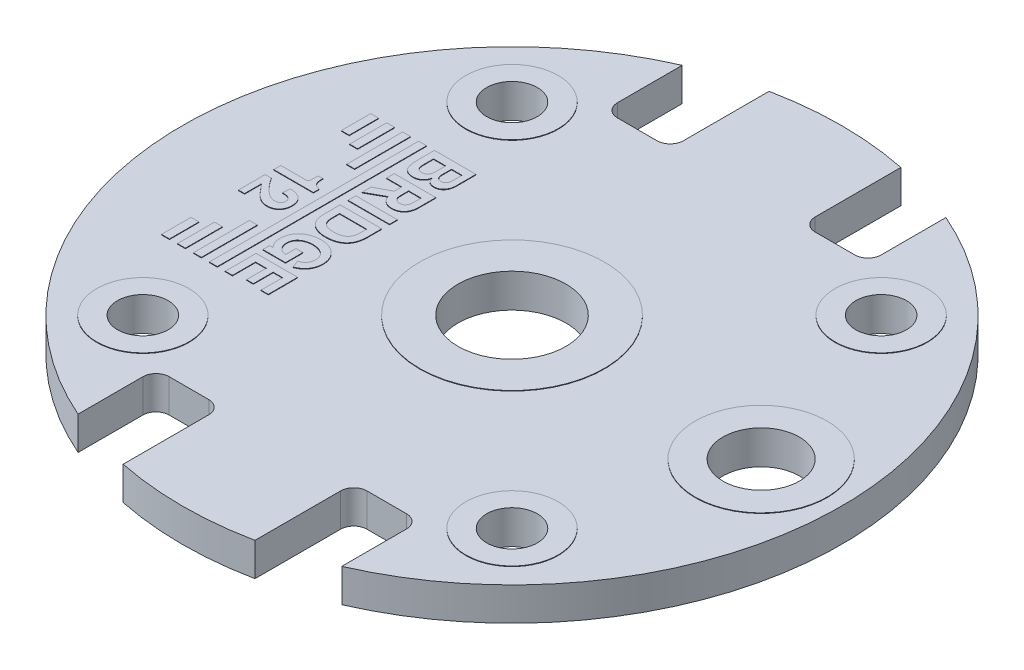
SolidWorks part; units mm, degrees
material "C110 COPPER"
ref_plane "Front Plane" through (0, 0, 0) normal (0, 0, 1) x (1, 0, 0)
ref_plane "Top Plane" through (0, 0, 0) normal (0, 1, 0) x (1, 0, 0)
ref_plane "Right Plane" through (0, 0, 0) normal (1, 0, 0) x (0, 0, -1)
sketch "Sketch1" plane through (0, 0, 0) normal (0, 1, 0) x (1, 0, 0)
  line L0 (-6.35, 14.5497) -> (-6.35, 11.43)
  line L1 (-5.715, 10.795) -> (-3.81, 10.795)
  line L2 (-3.175, 11.43) -> (-3.175, 15.5543)
  line L3 (0, 19.0474) -> (0, -17.3756) construction
  line L4 (-23.6625, 0) -> (27.7174, 0) construction
  line L5 (3.175, 11.43) -> (3.175, 15.5543)
  line L6 (5.715, 10.795) -> (3.81, 10.795)
  line L7 (6.35, 14.5497) -> (6.35, 11.43)
  line L8 (6.35, -14.5497) -> (6.35, -11.43)
  line L9 (5.715, -10.795) -> (3.81, -10.795)
  line L10 (3.175, -11.43) -> (3.175, -15.5543)
  line L11 (-3.175, -11.43) -> (-3.175, -15.5543)
  line L12 (-5.715, -10.795) -> (-3.81, -10.795)
  line L13 (-6.35, -14.5497) -> (-6.35, -11.43)
  arc A0 (-6.35, 14.5497) -> (-6.35, -14.5497) centre (0, 0) ccw
  arc A2 (-3.81, 10.795) -> (-3.175, 11.43) centre (-3.81, 11.43) ccw
  arc A3 (-6.35, 11.43) -> (-5.715, 10.795) centre (-5.715, 11.43) ccw
  arc A4 (3.81, 10.795) -> (3.175, 11.43) centre (3.81, 11.43) cw
  arc A5 (6.35, 11.43) -> (5.715, 10.795) centre (5.715, 11.43) cw
  arc A6 (6.35, -11.43) -> (5.715, -10.795) centre (5.715, -11.43) ccw
  arc A7 (3.81, -10.795) -> (3.175, -11.43) centre (3.81, -11.43) ccw
  arc A8 (-6.35, -11.43) -> (-5.715, -10.795) centre (-5.715, -11.43) cw
  arc A9 (-3.81, -10.795) -> (-3.175, -11.43) centre (-3.81, -11.43) cw
  arc A10 (3.175, 15.5543) -> (-3.175, 15.5543) centre (0, 0) ccw
  arc A11 (6.35, -14.5497) -> (6.35, 14.5497) centre (0, 0) ccw
  arc A12 (-3.175, -15.5543) -> (3.175, -15.5543) centre (0, 0) ccw
  dimension "D1" = 31.75
  dimension "D2" = 3.175
  dimension "D5" = 0.635
  dimension "D3" = 6.35
  dimension "D4" = 10.795
extrude "Boss-Extrude1" add sketch "Sketch1" along normal mid plane 1.6
sketch "Sketch12" plane through (0, 0.8, 0) normal (0, 1, 0) x (1, 0, 0)
  circle A0 centre (0, 0) radius 2.6
  dimension "D1" = 5.2
extrude "Cut-Extrude2" cut sketch "Sketch12" against normal through all
hole_wizard "#2 Clearance Hole1" positions "Sketch4" profile "Sketch5" hole size "#2" standard "ANSI Inch" end condition up to next
sketch "Sketch4" plane through (0, 0.8, 0) normal (0, 1, 0) x (1, 0, 0)
  line L1 (-8.89, 8.89) -> (8.89, 8.89)
  line L2 (-8.89, 8.89) -> (-8.89, -8.89)
  line L3 (-8.89, -8.89) -> (8.89, -8.89)
  line L4 (8.89, 8.89) -> (8.89, -8.89)
  line L5 (-8.89, 8.89) -> (8.89, -8.89) construction
  line L6 (-8.89, -8.89) -> (8.89, 8.89) construction
  point P1 (-8.89, 8.89)
  point P2 (8.89, -8.89)
  point P5 (-8.89, -8.89)
  point P6 (8.89, 8.89)
  point P70 (0, 0)
  dimension "D1" = 17.78
  dimension "D2" = 17.78
sketch "Sketch5" plane through (-8.89, 0.8, -8.89) normal (1, 0, 0) x (0, 0, 1)
  line L0 (0, 0) -> (0, 1.6)
  line L1 (0, 1.6) -> (1.2192, 1.6)
  line L2 (1.2192, 1.6) -> (1.2192, 0)
  line L5 (1.2192, 0) -> (0, 0)
  line L11 (0, -6.35) -> (0, 107.95) construction
  dimension "Thru Hole Dia." = 2.4384
  dimension "Thru Hole Depth" = 1.6
sketch "Sketch6" plane through (0, 0.8, 0) normal (0, 1, 0) x (1, 0, 0)
  line L0 (-21.8912, 0) -> (24.3968, 0) construction
  circle A3 centre (12, 0) radius 1.8415
  dimension "D1" = 3.683
  dimension "D2" = 12
extrude "Cut-Extrude1" cut sketch "Sketch6" against normal through all
sketch "Sketch8" plane through (0, 0.8, 0) normal (0, 1, 0) x (1, 0, 0)
  circle A0 centre (-8.89, 8.89) radius 2.2225
  circle A1 centre (8.89, 8.89) radius 2.2225
  circle A2 centre (-8.89, -8.89) radius 2.2225
  circle A3 centre (8.89, -8.89) radius 2.2225
  circle A4 centre (0, 0) radius 4.445
  circle A5 centre (12, 0) radius 3.175
  circle A19 centre (0, 0) radius 2.6 construction
  circle A20 centre (0, 0) radius 2.6
  circle A21 centre (-8.89, -8.89) radius 1.2192 construction
  circle A22 centre (-8.89, -8.89) radius 1.2192
  circle A23 centre (-8.89, 8.89) radius 1.2192 construction
  circle A24 centre (-8.89, 8.89) radius 1.2192
  circle A25 centre (8.89, 8.89) radius 1.2192 construction
  circle A26 centre (8.89, 8.89) radius 1.2192
  circle A27 centre (12, 0) radius 1.8415 construction
  circle A28 centre (12, 0) radius 1.8415
  circle A29 centre (8.89, -8.89) radius 1.2192 construction
  circle A30 centre (8.89, -8.89) radius 1.2192
  dimension "D1" = 4.445
  dimension "D2" = 8.89
  dimension "D3" = 6.35
extrude "Boss-Extrude6" add sketch "Sketch8" along normal blind 0.0254
sketch "Sketch10" plane through (0, 0.8, 0) normal (0, 1, 0) x (1, 0, 0)
  line L0 (-8.4106, 4.6318) -> (-8.4106, 4.143)
  line L1 (-7.8263, 4.1458) -> (-7.8263, 4.6318)
  line L2 (-7.8263, 4.6318) -> (-8.4106, 4.6318)
  line L3 (-7.5454, 4.6318) -> (-7.5454, 4.1852)
  line L4 (-7.0397, 4.1852) -> (-7.0397, 4.6318)
  line L5 (-7.0397, 4.6318) -> (-7.5454, 4.6318)
  line L6 (-6.7419, 5.0083) -> (-6.7419, 4.0672)
  line L7 (-7.6437, 3.8143) -> (-7.6494, 3.8143)
  line L8 (-8.7421, 4.1571) -> (-8.7421, 5.0083)
  line L9 (-8.7421, 5.0083) -> (-6.7419, 5.0083)
  line L10 (-7.6746, 2.6963) -> (-7.6746, 2.2861)
  line L11 (-7.0734, 2.3423) -> (-7.0734, 2.6963)
  line L12 (-7.0734, 2.6963) -> (-7.6746, 2.6963)
  line L13 (-6.7419, 3.0727) -> (-6.7419, 2.2384)
  line L14 (-7.9359, 1.9603) -> (-8.7421, 1.5136)
  line L15 (-8.7421, 1.5136) -> (-8.7421, 1.949)
  line L16 (-8.7421, 1.949) -> (-8.0061, 2.3367)
  line L17 (-8.0061, 2.3367) -> (-8.0061, 2.6963)
  line L18 (-8.0061, 2.6963) -> (-8.7421, 2.6963)
  line L19 (-8.7421, 2.6963) -> (-8.7421, 3.0727)
  line L20 (-8.7421, 3.0727) -> (-6.7419, 3.0727)
  line L21 (-6.7419, 1.2215) -> (-6.7419, 0.8451)
  line L22 (-6.7419, 0.8451) -> (-8.7421, 0.8451)
  line L23 (-8.7421, 0.8451) -> (-8.7421, 1.2215)
  line L24 (-8.7421, 1.2215) -> (-6.7419, 1.2215)
  line L25 (-8.3938, 0.0894) -> (-8.3938, -0.2534)
  line L26 (-7.0903, -0.2449) -> (-7.0903, 0.0894)
  line L27 (-7.0903, 0.0894) -> (-8.3938, 0.0894)
  line L28 (-6.7419, 0.4658) -> (-6.7419, -0.2365)
  line L29 (-8.7421, -0.3068) -> (-8.7421, 0.4658)
  line L30 (-8.7421, 0.4658) -> (-6.7419, 0.4658)
  line L31 (-7.9808, -2.9175) -> (-7.9808, -2.423)
  line L32 (-7.9808, -2.423) -> (-7.6494, -2.423)
  line L33 (-7.6494, -2.423) -> (-7.6494, -3.2602)
  line L34 (-7.6494, -3.2602) -> (-8.7421, -3.2602)
  line L35 (-8.7421, -3.2602) -> (-8.7421, -2.9343)
  line L36 (-8.7421, -2.9343) -> (-8.5708, -2.9343)
  line L37 (-7.2785, -3.2602) -> (-7.4218, -2.909)
  line L38 (-6.7419, -3.5807) -> (-6.7419, -4.9965)
  line L39 (-6.7419, -4.9965) -> (-7.0903, -4.9965)
  line L40 (-7.0903, -4.9965) -> (-7.0903, -3.9571)
  line L41 (-7.0903, -3.9571) -> (-7.5454, -3.9571)
  line L42 (-7.5454, -3.9571) -> (-7.5454, -4.9123)
  line L43 (-7.5454, -4.9123) -> (-7.8769, -4.9123)
  line L44 (-7.8769, -4.9123) -> (-7.8769, -3.9571)
  line L45 (-7.8769, -3.9571) -> (-8.3938, -3.9571)
  line L46 (-8.3938, -3.9571) -> (-8.3938, -5.0696)
  line L47 (-8.3938, -5.0696) -> (-8.7421, -5.0696)
  line L48 (-8.7421, -5.0696) -> (-8.7421, -3.5807)
  line L49 (-8.7421, -3.5807) -> (-6.7419, -3.5807)
  line L50 (-10.4829, 0.8387) -> (-10.4829, 1.1421)
  line L51 (-10.4829, 1.1421) -> (-10.2525, 1.1421)
  line L52 (-10.2525, 1.1421) -> (-10.2525, 1.0859)
  line L53 (-9.9014, 0.6168) -> (-9.9014, 0.3358)
  line L54 (-9.9014, 0.3358) -> (-11.8117, 0.3358)
  line L55 (-11.8117, 0.3358) -> (-11.8117, 0.6786)
  line L56 (-11.8117, 0.6786) -> (-10.6711, 0.6786)
  line L57 (-11.5139, -0.5406) -> (-11.5139, -1.3665)
  line L58 (-11.5139, -1.3665) -> (-11.8117, -1.3665)
  line L59 (-11.8117, -1.3665) -> (-11.8117, -0.0743)
  line L60 (-11.8117, -0.0743) -> (-11.5139, -0.0743)
  line L61 (-10.6318, -0.417) -> (-10.6065, -0.0743)
  line L62 (-9.8937, -2.3704) -> (-10.2778, -2.3704)
  line L63 (-10.2778, -2.3704) -> (-10.2778, -5.068)
  line L64 (-10.2778, -5.068) -> (-9.8937, -5.068)
  line L65 (-9.8937, -5.068) -> (-9.8937, -2.3704)
  line L66 (-10.6619, -3.283) -> (-11.0461, -3.283)
  line L67 (-11.0461, -3.283) -> (-11.0461, -5.068)
  line L68 (-11.0461, -5.068) -> (-10.6619, -5.068)
  line L69 (-10.6619, -5.068) -> (-10.6619, -3.283)
  line L70 (-11.4303, -3.6479) -> (-11.8144, -3.6479)
  line L71 (-11.8144, -3.6479) -> (-11.8144, -5.068)
  line L72 (-11.8144, -5.068) -> (-11.4303, -5.068)
  line L73 (-11.4303, -5.068) -> (-11.4303, -3.6479)
  line L74 (-9.8937, 5.0104) -> (-10.2778, 5.0104)
  line L75 (-10.2778, 5.0104) -> (-10.2778, 2.3128)
  line L76 (-10.2778, 2.3128) -> (-9.8937, 2.3128)
  line L77 (-9.8937, 2.3128) -> (-9.8937, 5.0104)
  line L78 (-10.6619, 5.0104) -> (-11.0461, 5.0104)
  line L79 (-11.0461, 5.0104) -> (-11.0461, 3.2254)
  line L80 (-11.0461, 3.2254) -> (-10.6619, 3.2254)
  line L81 (-10.6619, 3.2254) -> (-10.6619, 5.0104)
  line L82 (-11.4303, 5.0104) -> (-11.8144, 5.0104)
  line L83 (-11.8144, 5.0104) -> (-11.8144, 3.5904)
  line L84 (-11.8144, 3.5904) -> (-11.4303, 3.5904)
  line L85 (-11.4303, 3.5904) -> (-11.4303, 5.0104)
  line L86 (-9.1255, 5.0104) -> (-9.5095, 5.0104)
  line L87 (-9.5095, 5.0104) -> (-9.5095, -5.0679)
  line L88 (-9.5095, -5.0679) -> (-9.1255, -5.0679)
  line L89 (-9.1255, -5.0679) -> (-9.1255, 5.0104)
  spline S0 degree 3 poles (-8.4106, 4.143) (-8.4106, 3.9155) (-8.3404, 3.7778) (-8.1325, 3.7778) knots 1 1 1 1 2 2 2 2
  spline S1 degree 3 poles (-8.1325, 3.7778) (-7.9078, 3.7778) (-7.8263, 3.9183) (-7.8263, 4.1458) knots 2 2 2 2 3 3 3 3
  spline S2 degree 3 poles (-7.5454, 4.1852) (-7.5454, 4.0194) (-7.4808, 3.8677) (-7.2898, 3.8677) knots 1 1 1 1 2 2 2 2
  spline S3 degree 3 poles (-7.2898, 3.8677) (-7.1381, 3.8677) (-7.0397, 3.9661) (-7.0397, 4.1852) knots 2 2 2 2 3 3 3 3
  spline S4 degree 3 poles (-6.7419, 4.0672) (-6.7419, 3.7385) (-6.9077, 3.4744) (-7.2392, 3.4744) knots 1 1 1 1 2 2 2 2
  spline S5 degree 3 poles (-7.2392, 3.4744) (-7.4583, 3.4744) (-7.6016, 3.5952) (-7.6437, 3.8143) knots 2 2 2 2 3 3 3 3
  spline S6 degree 3 poles (-7.6494, 3.8143) (-7.6774, 3.539) (-7.905, 3.3845) (-8.1438, 3.3845) knots 4 4 4 4 5 5 5 5
  spline S7 degree 3 poles (-8.1438, 3.3845) (-8.6438, 3.3845) (-8.7421, 3.7413) (-8.7421, 4.1571) knots 5 5 5 5 6 6 6 6
  spline S8 degree 3 poles (-7.6746, 2.2861) (-7.6746, 2.0951) (-7.5623, 1.9575) (-7.374, 1.9575) knots 1 1 1 1 2 2 2 2
  spline S9 degree 3 poles (-7.374, 1.9575) (-7.1914, 1.9575) (-7.0734, 2.0811) (-7.0734, 2.3423) knots 2 2 2 2 3 3 3 3
  spline S10 degree 3 poles (-6.7419, 2.2384) (-6.7419, 1.8142) (-6.9948, 1.5642) (-7.3459, 1.5642) knots 1 1 1 1 2 2 2 2
  spline S11 degree 3 poles (-7.3459, 1.5642) (-7.7954, 1.5642) (-7.8994, 1.8648) (-7.9359, 1.9603) knots 2 2 2 2 3 3 3 3
  spline S12 degree 3 poles (-8.3938, -0.2534) (-8.3938, -0.6242) (-8.259, -0.8265) (-7.7421, -0.8265) knots 1 1 1 1 2 2 2 2
  spline S13 degree 3 poles (-7.7421, -0.8265) (-7.3488, -0.8265) (-7.0903, -0.6551) (-7.0903, -0.2449) knots 2 2 2 2 3 3 3 3
  spline S14 degree 3 poles (-6.7419, -0.2365) (-6.7419, -0.9276) (-7.169, -1.2198) (-7.7421, -1.2198) knots 1 1 1 1 2 2 2 2
  spline S15 degree 3 poles (-7.7421, -1.2198) (-8.3938, -1.2198) (-8.7421, -0.9023) (-8.7421, -0.3068) knots 2 2 2 2 3 3 3 3
  spline S16 degree 3 poles (-7.4218, -2.909) (-7.2617, -2.8669) (-7.0397, -2.7405) (-7.0397, -2.409) knots 0 0 0 0 1 1 1 1
  spline S17 degree 3 poles (-7.0397, -2.409) (-7.0397, -2.0101) (-7.3937, -1.8443) (-7.7421, -1.8443) knots 1 1 1 1 2 2 2 2
  spline S18 degree 3 poles (-7.7421, -1.8443) (-8.0904, -1.8443) (-8.4444, -2.0101) (-8.4444, -2.409) knots 2 2 2 2 3 3 3 3
  spline S19 degree 3 poles (-8.4444, -2.409) (-8.4444, -2.6759) (-8.2561, -2.9175) (-7.9808, -2.9175) knots 3 3 3 3 4 4 4 4
  spline S20 degree 3 poles (-8.5708, -2.9343) (-8.7197, -2.8023) (-8.7927, -2.5832) (-8.7927, -2.409) knots 10 10 10 10 11 11 11 11
  spline S21 degree 3 poles (-8.7927, -2.409) (-8.7927, -1.7685) (-8.3067, -1.451) (-7.7421, -1.451) knots 11 11 11 11 12 12 12 12
  spline S22 degree 3 poles (-7.7421, -1.451) (-7.1774, -1.451) (-6.6914, -1.8106) (-6.6914, -2.409) knots 12 12 12 12 13 13 13 13
  spline S23 degree 3 poles (-6.6914, -2.409) (-6.6914, -2.8163) (-6.8965, -3.1085) (-7.2785, -3.2602) knots 13 13 13 13 14 14 14 14
  spline S24 degree 3 poles (-10.6711, 0.6786) (-10.5194, 0.6786) (-10.4829, 0.7066) (-10.4829, 0.8387) knots 0 0 0 0 1 1 1 1
  spline S25 degree 3 poles (-10.2525, 1.0859) (-10.2525, 0.746) (-10.1121, 0.6645) (-9.9014, 0.6168) knots 4 4 4 4 5 5 5 5
  spline S26 degree 3 poles (-10.6065, -0.0743) (-10.1711, -0.0743) (-9.8677, -0.2681) (-9.8677, -0.7317) knots 0 0 0 0 1 1 1 1
  spline S27 degree 3 poles (-9.8677, -0.7317) (-9.8677, -1.094) (-10.098, -1.3385) (-10.4605, -1.3385) knots 1 1 1 1 2 2 2 2
  spline S28 degree 3 poles (-10.4605, -1.3385) (-10.9633, -1.3385) (-11.2274, -0.8805) (-11.5139, -0.5406) knots 2 2 2 2 3 3 3 3
  spline S29 degree 3 poles (-11.5139, -0.0743) (-11.3482, -0.3496) (-10.8959, -0.9452) (-10.4914, -0.9452) knots 7 7 7 7 8 8 8 8
  spline S30 degree 3 poles (-10.4914, -0.9452) (-10.3396, -0.9452) (-10.1992, -0.8946) (-10.1992, -0.6895) knots 8 8 8 8 9 9 9 9
  spline S31 degree 3 poles (-10.1992, -0.6895) (-10.1992, -0.4816) (-10.3705, -0.417) (-10.6318, -0.417) knots 9 9 9 9 10 10 10 10
extrude "Boss-Extrude7" add sketch "Sketch10" along normal blind 0.0254
